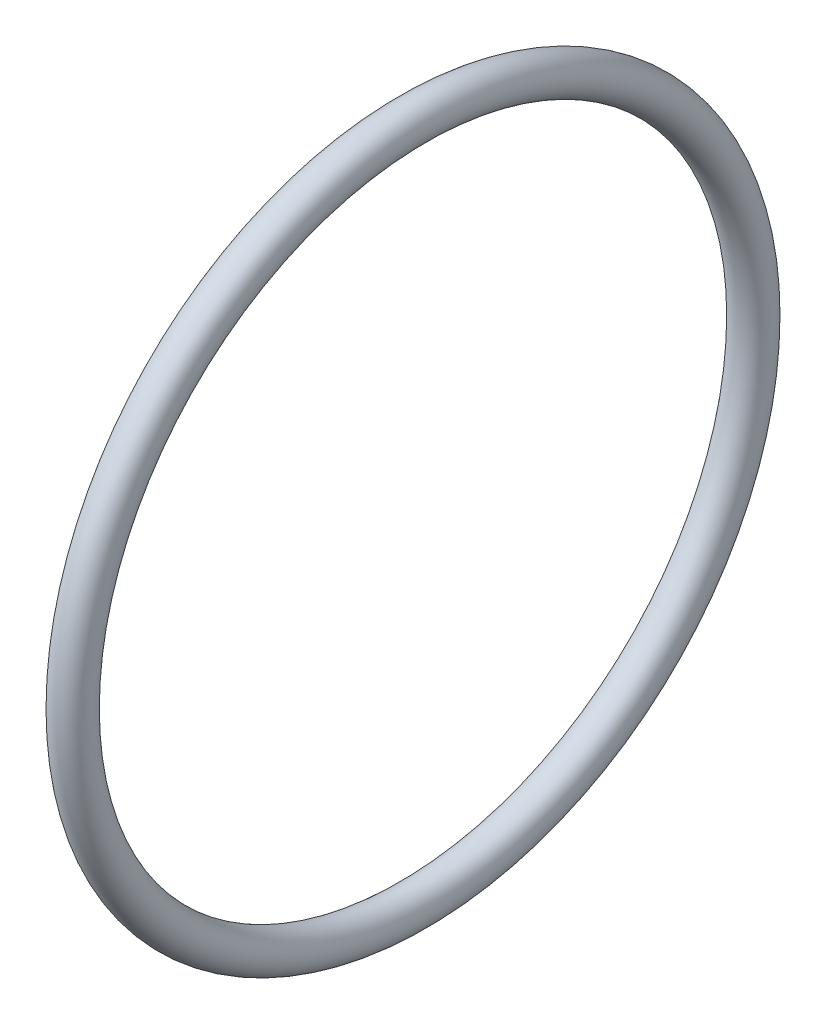
SolidWorks part; units mm, degrees
material "EPDM durômetro 60"
ref_plane "Plano frontal" through (0, 0, 0) normal (0, 0, 1) x (1, 0, 0)
ref_plane "Plano superior" through (0, 0, 0) normal (0, 1, 0) x (1, 0, 0)
ref_plane "Plano direito" through (0, 0, 0) normal (1, 0, 0) x (0, 0, -1)
sketch "Esboço1" plane through (0, 0, 0) normal (0, 0, 1) x (1, 0, 0)
  line L0 (0, 0) -> (-9192.9557, 0) construction
  line L1 (0, -183.8591) -> (0, 9009.0966) construction
  circle A0 centre (0, 27.075) radius 1.5
  point P7 (0, 28.575)
  point P8 (0, 28.575)
  dimension "D1" = 3
  dimension "D2" = 28.575
revolve "Revolução1" add sketch "Esboço1" angle 360 about L0
